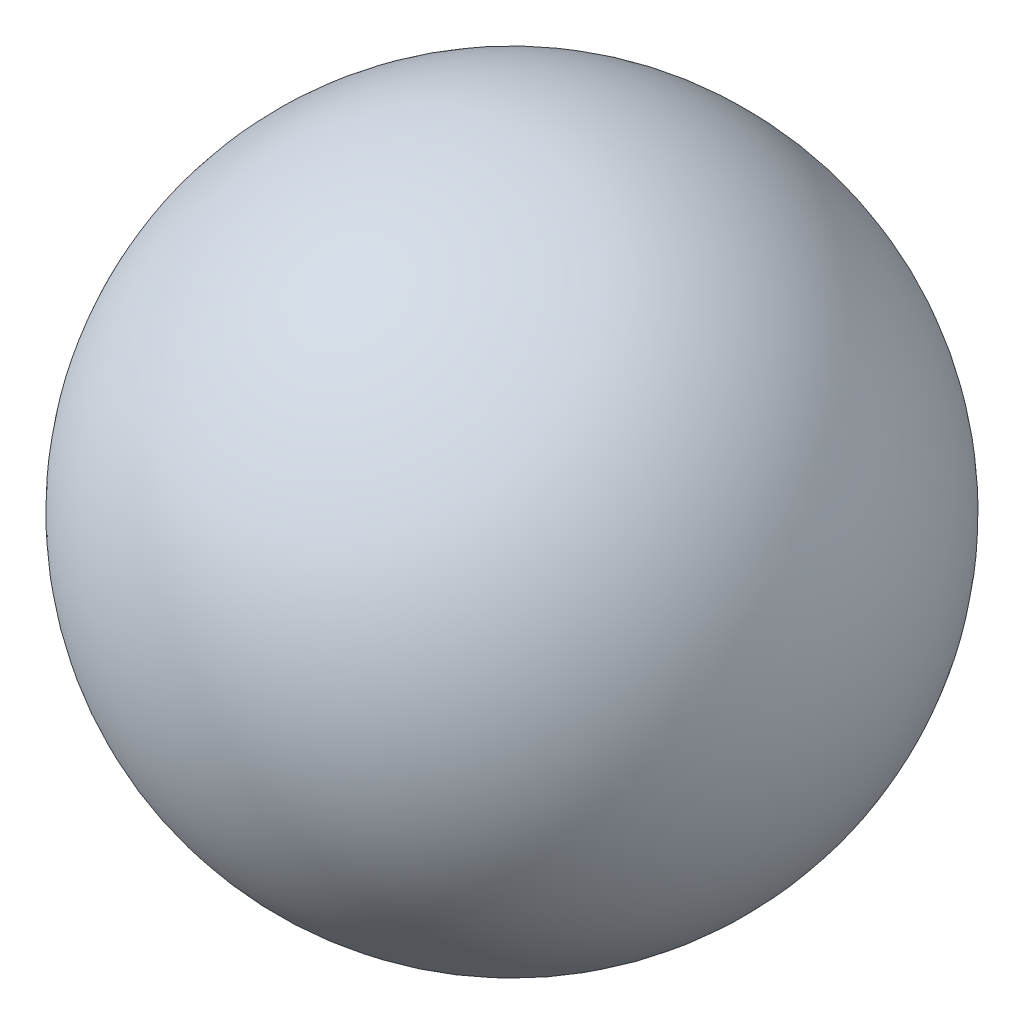
SolidWorks part; units mm, degrees
ref_plane "Front Plane" through (0, 0, 0) normal (0, 0, 1) x (1, 0, 0)
ref_plane "Top Plane" through (0, 0, 0) normal (0, 1, 0) x (1, 0, 0)
ref_plane "Right Plane" through (0, 0, 0) normal (1, 0, 0) x (0, 0, -1)
sketch "Sketch1" plane through (0, 0, 0) normal (0, 0, 1) x (1, 0, 0)
  line L0 (-44.45, 0) -> (44.45, 0)
  arc A0 (44.45, 0) -> (-44.45, 0) centre (0, 0) ccw
  dimension "D1" = 88.9
revolve "Revolve1" add sketch "Sketch1" angle 360 about L0
sketch "Sketch2" plane through (0, 0, 0) normal (0, 0, 1) x (1, 0, 0)
  line L0 (-1000, 0) -> (49000, 0) construction
  line L1 (0, -1000) -> (0, 49000) construction
  line L2 (0, 0) -> (-38.4948, 22.225)
  line L3 (0, 0) -> (-38.4948, -22.225)
  line L4 (0, 0) -> (-42.9354, 11.5045)
  line L5 (0, 0) -> (-41.0664, 17.0103)
  circle A0 centre (0, 0) radius 44.45 construction
  dimension "D1" = 30
  dimension "D2" = 15
  dimension "D3" = 7.5
